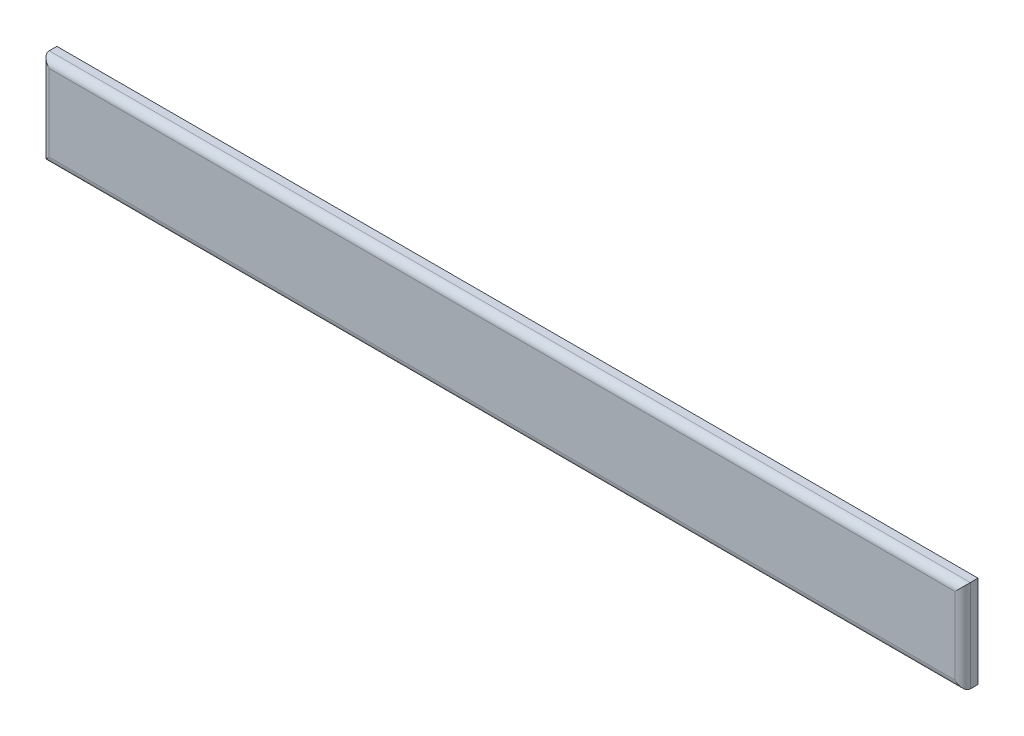
SolidWorks part; units mm, degrees
ref_plane "Front Plane" through (0, 0, 0) normal (0, 0, 1) x (1, 0, 0)
ref_plane "Top Plane" through (0, 0, 0) normal (0, 1, 0) x (1, 0, 0)
ref_plane "Right Plane" through (0, 0, 0) normal (1, 0, 0) x (0, 0, -1)
sketch "Sketch1" plane through (0, 0, 0) normal (0, 0, 1) x (1, 0, 0)
  line L1 (-3000, -300) -> (3000, -300)
  line L2 (-3000, -300) -> (-3000, 300)
  line L3 (-3000, 300) -> (3000, 300)
  line L4 (3000, -300) -> (3000, 300)
  line L5 (-3000, -300) -> (3000, 300) construction
  line L6 (-3000, 300) -> (3000, -300) construction
  point P0 (0, 0)
  dimension "D1" = 600
  dimension "D2" = 6000
extrude "Boss-Extrude1" add sketch "Sketch1" against normal blind 100
fillet "Fillet1" radius 50 4 edges at (0, -300, 0) (-3000, 0, 0) (0, 300, 0) (3000, 0, 0)
